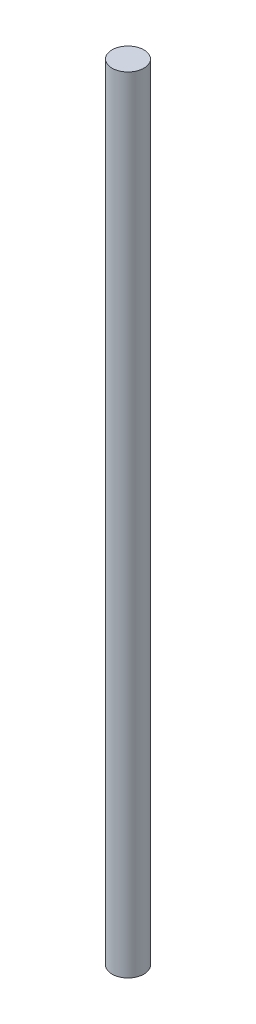
SolidWorks part; units mm, degrees
ref_plane "Front Plane" through (0, 0, 0) normal (0, 0, 1) x (1, 0, 0)
ref_plane "Top Plane" through (0, 0, 0) normal (0, 1, 0) x (1, 0, 0)
ref_plane "Right Plane" through (0, 0, 0) normal (1, 0, 0) x (0, 0, -1)
sketch "Sketch1" plane through (0, 0, 0) normal (0, 1, 0) x (1, 0, 0)
  circle A0 centre (0, 0) radius 1.5
  dimension "D1" = 3
extrude "Boss-Extrude1" add sketch "Sketch1" along normal blind 74
